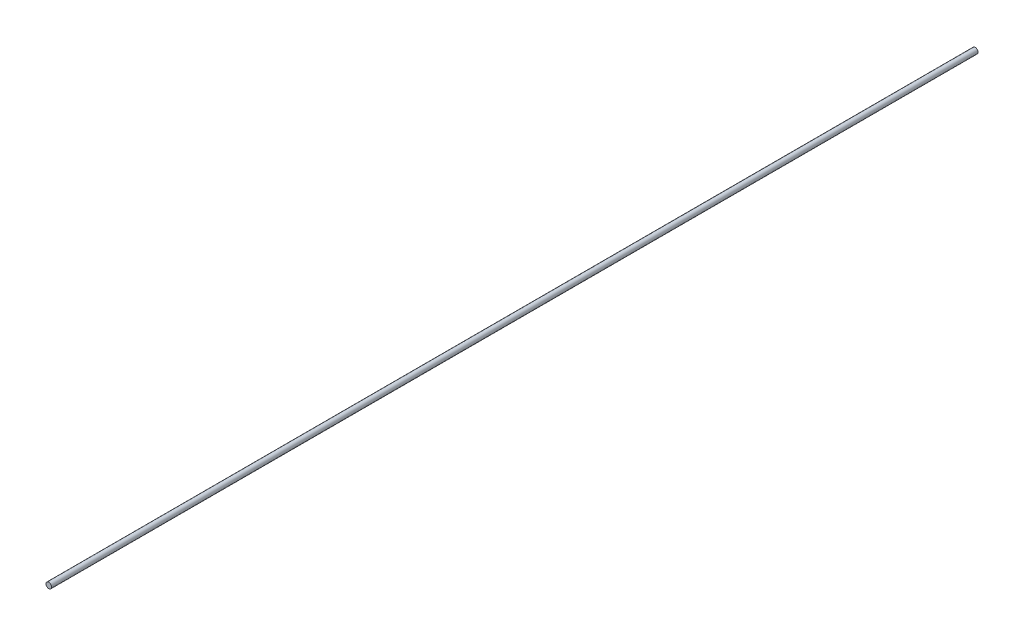
SolidWorks part; units mm, degrees
ref_plane "Front" through (0, 0, 0) normal (0, 0, 1) x (1, 0, 0)
ref_plane "Top" through (0, 0, 0) normal (0, 1, 0) x (1, 0, 0)
ref_plane "Right" through (0, 0, 0) normal (1, 0, 0) x (0, 0, -1)
sketch "Sketch1" plane through (0, 0, 0) normal (0, 0, 1) x (1, 0, 0)
  circle A0 centre (0, 0) radius 0.4826
  dimension "D1" = 0.9652
extrude "Boss-Extrude1" add sketch "Sketch1" along normal blind 160
